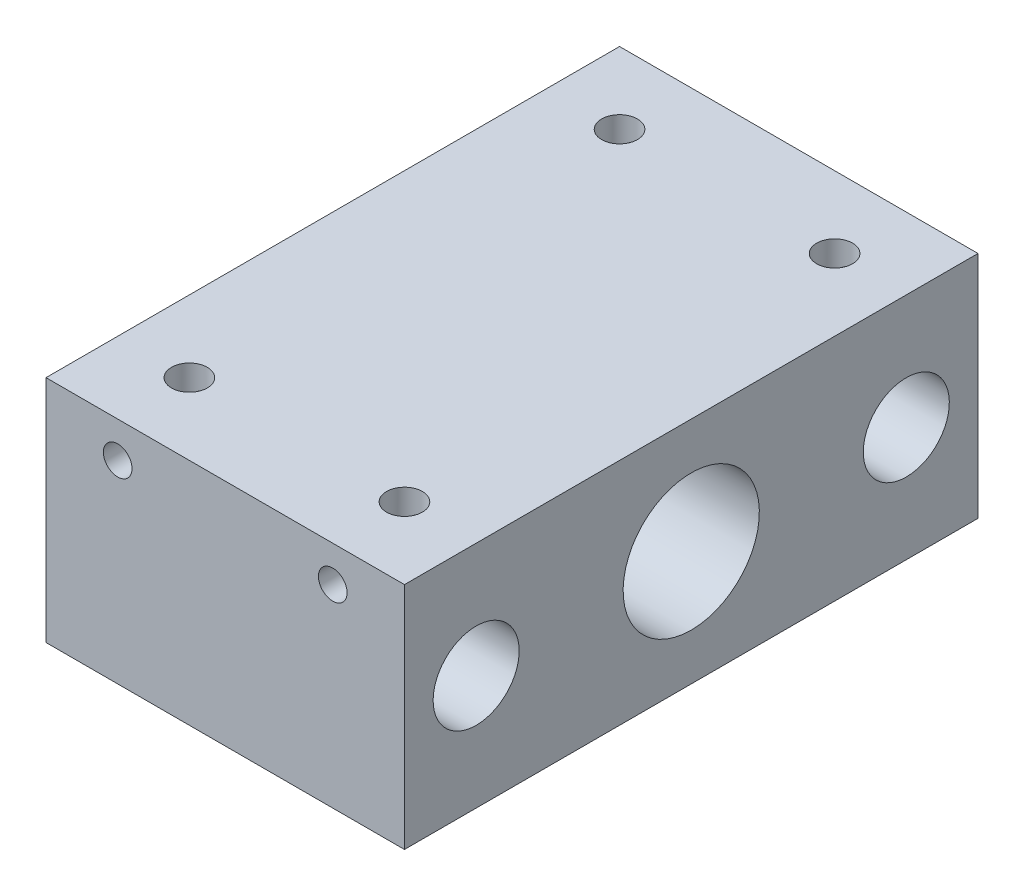
SolidWorks part; units mm, degrees
ref_plane "前视基准面" through (0, 0, 0) normal (0, 0, 1) x (1, 0, 0)
ref_plane "上视基准面" through (0, 0, 0) normal (0, 1, 0) x (1, 0, 0)
ref_plane "右视基准面" through (0, 0, 0) normal (1, 0, 0) x (0, 0, -1)
sketch "草图1" plane through (0, 0, 0) normal (0, 0, 1) x (1, 0, 0)
  line L0 (-34.8881, 7.8731) -> (54.1045, 7.8731) construction
  line L1 (-24.4403, 12.8731) -> (25.5597, 12.8731)
  line L2 (-24.4403, 12.8731) -> (-24.4403, -19.1269)
  line L3 (-24.4403, -19.1269) -> (25.5597, -19.1269)
  line L4 (25.5597, 12.8731) -> (25.5597, -19.1269)
  line L5 (0.5597, 41.9776) -> (0.5597, -40.4851) construction
  circle A0 centre (-14.4403, 7.8731) radius 2
  circle A1 centre (15.5597, 7.8731) radius 2
  dimension "D4" = 4
  dimension "D5" = 30
  dimension "D1" = 50
  dimension "D2" = 32
  dimension "D3" = 5
extrude "凸台-拉伸1" add sketch "草图1" along normal blind 80
sketch "草图2" plane through (0, 12.8731, 0) normal (0, 1, 0) x (1, 0, 0)
  line L0 (-38.9859, -40) -> (41.0621, -40) construction
  line L1 (0.5597, 24.8757) -> (0.5597, -98.3855) construction
  line L2 (25.5597, -80) -> (25.5597, 0) construction
  line L3 (-24.4403, -80) -> (-24.4403, 0) construction
  line L4 (25.5597, 0) -> (-24.4403, 0) construction
  line L5 (25.5597, -80) -> (-24.4403, -80) construction
  circle A0 centre (-14.4403, -10) radius 2.5
  circle A1 centre (15.5597, -10) radius 2.5
  circle A2 centre (15.5597, -70) radius 2.5
  circle A3 centre (-14.4403, -70) radius 2.5
  dimension "D1" = 60
  dimension "D2" = 30
  dimension "D3" = 5
extrude "切除-拉伸1" cut sketch "草图2" against normal blind 80
sketch "草图3" plane through (-24.4403, 0, 0) normal (-1, 0, 0) x (0, 0, 1)
  line L0 (-2.3406, -3.1269) -> (84.3161, -3.1269) construction
  line L1 (40, 34.049) -> (40, -45.3027) construction
  line L2 (0, 12.8731) -> (0, -19.1269) construction
  line L3 (80, 12.8731) -> (80, -19.1269) construction
  line L4 (80, 12.8731) -> (0, 12.8731) construction
  line L5 (80, -19.1269) -> (0, -19.1269) construction
  circle A0 centre (10, -3.1269) radius 6
  circle A1 centre (70, -3.1269) radius 6
  circle A2 centre (40, -3.1269) radius 9.5
  dimension "D1" = 12
  dimension "D2" = 19
  dimension "D3" = 60
extrude "切除-拉伸7" cut sketch "草图3" against normal blind 80
